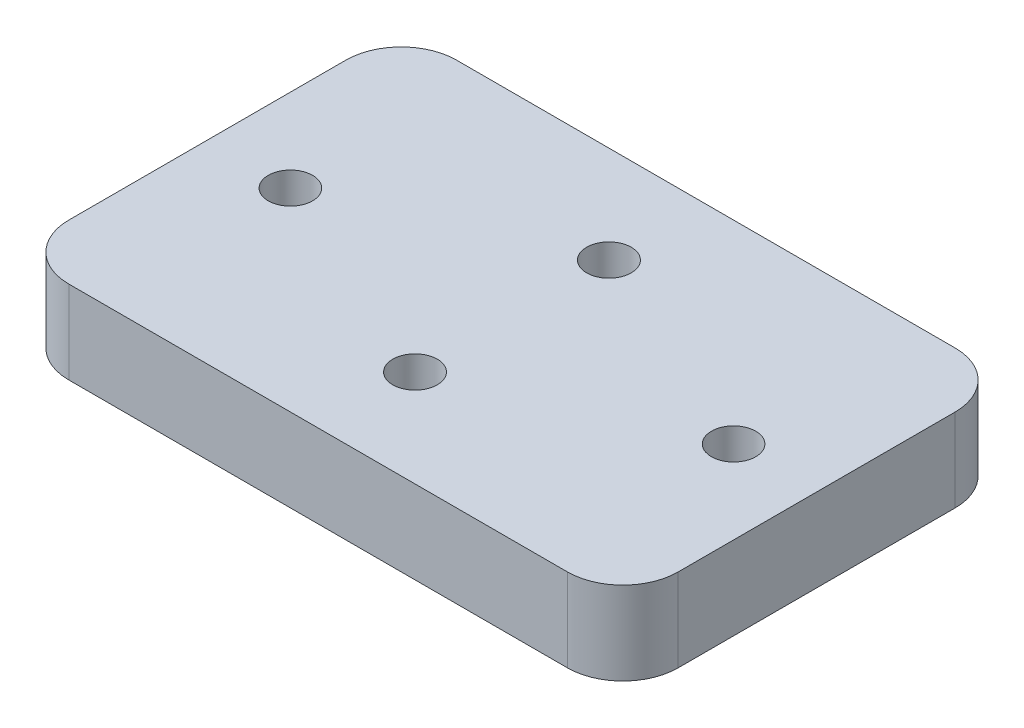
SolidWorks part; units mm, degrees
material "6061-T6 (SS)"
ref_plane "Front Plane" through (0, 0, 0) normal (0, 0, 1) x (1, 0, 0)
ref_plane "Top Plane" through (0, 0, 0) normal (0, 1, 0) x (1, 0, 0)
ref_plane "Right Plane" through (0, 0, 0) normal (1, 0, 0) x (0, 0, -1)
sketch "Sketch1" plane through (0, 0, 0) normal (0, 1, 0) x (1, 0, 0)
  line L0 (31.75, 0) -> (-31.75, 0) construction
  line L1 (-34.925, 22.225) -> (34.925, 22.225)
  line L2 (-34.925, 22.225) -> (-34.925, -22.225)
  line L3 (-34.925, -22.225) -> (34.925, -22.225)
  line L4 (34.925, 22.225) -> (34.925, -22.225)
  line L5 (-34.925, 22.225) -> (34.925, -22.225) construction
  line L6 (-34.925, -22.225) -> (34.925, 22.225) construction
  line L7 (-31.75, 6.35) -> (-21.2985, 6.35) construction
  line L8 (-31.75, 6.35) -> (-31.75, -6.35) construction
  line L9 (-31.75, -6.35) -> (-21.2985, -6.35) construction
  line L10 (31.75, 6.35) -> (31.75, -6.35) construction
  line L11 (21.2985, 6.35) -> (31.75, 6.35) construction
  line L12 (21.2985, -6.35) -> (31.75, -6.35) construction
  arc A0 (-21.2985, -6.35) -> (21.2985, -6.35) centre (0, 0) ccw construction
  arc A1 (-21.2985, -6.35) -> (21.2985, -6.35) centre (0, 0) ccw construction
  arc A2 (21.2985, 6.35) -> (-21.2985, 6.35) centre (0, 0) ccw construction
  arc A3 (21.2985, 6.35) -> (-21.2985, 6.35) centre (0, 0) ccw construction
  point P19 (0, 0)
  dimension "D1" = 44.45
  dimension "D2" = 69.85
  dimension "D4" = 12.7
  dimension "D5" = 63.5
extrude "Boss-Extrude1" add sketch "Sketch1" along normal blind 9.525
hole_wizard "CSK for #10 Flat Head Machine Screw (100)1" positions "Sketch2" profile "Sketch4" countersink size "#10" standard "ANSI Inch" end condition through all
sketch "Sketch2" plane through (0, 0, 0) normal (0, -1, 0) x (-1, 0, 0)
  line L5 (0, 11.1125) -> (0, 0) construction
  line L6 (0, 0) -> (0, -11.1125) construction
  line L7 (0, 22.225) -> (0, 11.1125) construction
  line L8 (-34.925, 22.225) -> (34.925, 22.225) construction
  line L10 (0, -11.1125) -> (0, -22.225) construction
  line L11 (34.925, -22.225) -> (-34.925, -22.225) construction
  point P179 (0, 11.1125)
  point P181 (0, -11.1125)
sketch "Sketch4" plane through (0, 0, -11.1125) normal (1, 0, 0) x (0, 0, -1)
  line L0 (0, 0) -> (0, 9.525)
  line L1 (0, 9.525) -> (2.5527, 9.525)
  line L2 (2.5527, 9.525) -> (2.5527, 2.6882)
  line L3 (2.5527, 2.6882) -> (4.8895, 0)
  line L5 (4.8895, 0) -> (0, 0)
  line L6 (-2.5527, 2.6882) -> (-4.8895, 0) construction
  line L11 (0, -6.35) -> (0, 107.95) construction
  dimension "Thru Hole Dia." = 5.1054
  dimension "Thru Hole Depth" = 9.525
  dimension "Near C'Sink Dia." = 9.779
  dimension "Near C'Sink Angle" = 82
hole_wizard "#10 (0.2) Diameter Hole1" positions "Sketch7" profile "Sketch8" hole size "#10" standard "ANSI Inch" end condition through all
sketch "Sketch7" plane through (0, 0, 0) normal (0, -1, 0) x (-1, 0, 0)
  line L0 (0, 0) -> (-25.4, 0) construction
  point P0 (-25.4, 0)
  dimension "D1" = 25.4
sketch "Sketch8" plane through (25.4, 0, 0) normal (1, 0, 0) x (0, 0, -1)
  line L0 (0, 0) -> (0, 9.525)
  line L1 (0, 9.525) -> (2.54, 9.525)
  line L2 (2.54, 9.525) -> (2.54, 0)
  line L5 (2.54, 0) -> (0, 0)
  line L11 (0, -6.35) -> (0, 107.95) construction
  dimension "Thru Hole Dia." = 5.08
  dimension "Thru Hole Depth" = 9.525
fillet "Fillet3" [suppressed] radius 3.175
mirror "Mirror1" about plane through (0, 0, 0) normal (1, 0, 0) of "#10 (0.2) Diameter Hole1"
sketch "Sketch9" plane through (0, 0, -22.225) normal (0, 0, -1) x (-1, 0, 0)
  line L0 (0, 6.35) -> (0, 9.525) construction
  line L1 (-34.925, 9.525) -> (34.925, 9.525) construction
  circle A0 centre (0, 28.575) radius 22.225
  dimension "D1" = 44.45
  dimension "D2" = 3.175
extrude "Cut-Extrude1" [suppressed] cut sketch "Sketch9" against normal through all
fillet "Fillet4" radius 6.35 4 edges at (-34.925, 4.7625, 22.225) (34.925, 4.7625, 22.225) (34.925, 4.7625, -22.225) (-34.925, 4.7625, -22.225)
